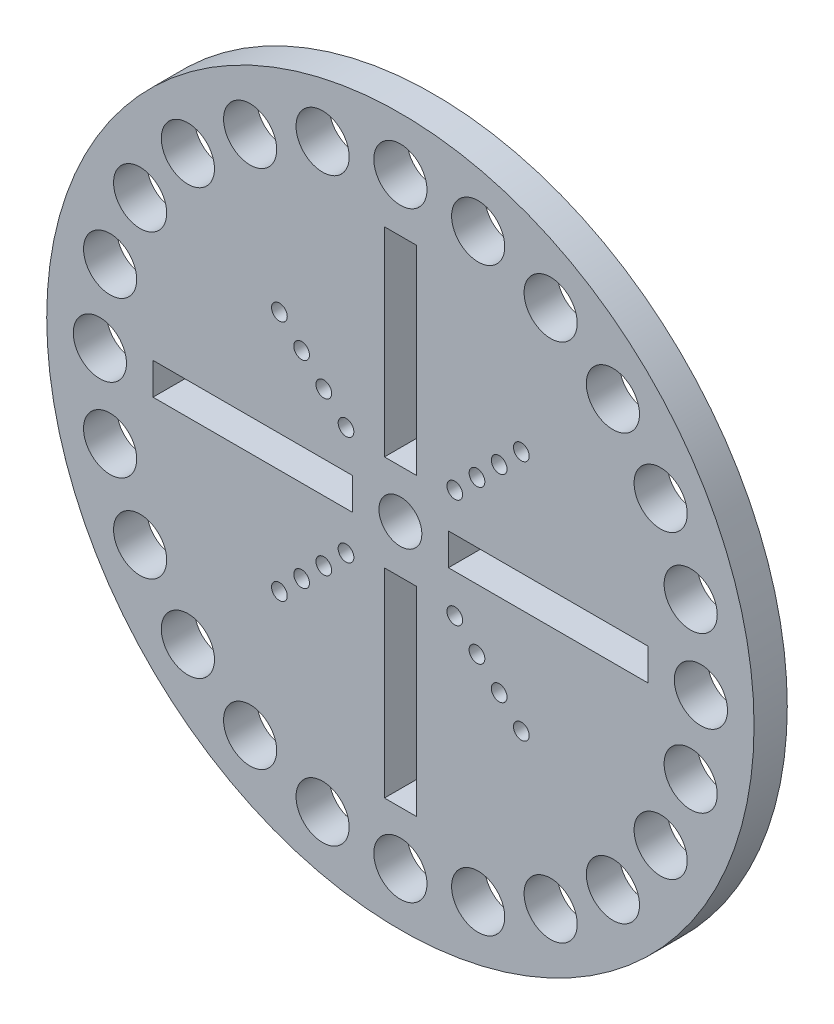
SolidWorks part; units mm, degrees
ref_plane "Front Plane" through (0, 0, 0) normal (0, 0, 1) x (1, 0, 0)
ref_plane "Top Plane" through (0, 0, 0) normal (0, 1, 0) x (1, 0, 0)
ref_plane "Right Plane" through (0, 0, 0) normal (1, 0, 0) x (0, 0, -1)
sketch "Sketch1" plane through (0, 0, 0) normal (0, 0, 1) x (1, 0, 0)
  line L0 (0, 31.26) -> (0, 33.8) construction
  line L1 (0, 28.72) -> (2.5183, 28.3885) construction
  line L2 (2.5183, 28.3885) -> (4.915, 28.0729) construction
  line L3 (4.915, 28.0729) -> (7.4333, 27.7414) construction
  line L4 (0, 2.05) -> (0, 4.59) construction
  line L5 (-0.1778, 26.1862) -> (0.1778, 26.1862) construction
  line L6 (-0.1778, 26.1862) -> (-0.1778, 30.9862) construction
  line L7 (-0.1778, 30.9862) -> (0.1778, 30.9862) construction
  line L8 (0.1778, 26.1862) -> (0.1778, 30.9862) construction
  line L9 (-1.524, 23.64) -> (1.524, 23.64)
  line L10 (-1.524, 23.64) -> (-1.524, 4.59)
  line L11 (-1.524, 4.59) -> (1.524, 4.59)
  line L12 (1.524, 23.64) -> (1.524, 4.59)
  line L13 (0, 26.18) -> (0, 23.64) construction
  line L14 (23.64, 1.524) -> (23.64, -1.524)
  line L15 (23.64, 1.524) -> (4.59, 1.524)
  line L16 (23.64, -1.524) -> (4.59, -1.524)
  line L17 (4.59, 1.524) -> (4.59, -1.524)
  line L18 (1.524, -23.64) -> (-1.524, -23.64)
  line L19 (1.524, -23.64) -> (1.524, -4.59)
  line L20 (-1.524, -23.64) -> (-1.524, -4.59)
  line L21 (1.524, -4.59) -> (-1.524, -4.59)
  line L22 (-23.64, -1.524) -> (-23.64, 1.524)
  line L23 (-23.64, -1.524) -> (-4.59, -1.524)
  line L24 (-23.64, 1.524) -> (-4.59, 1.524)
  line L25 (-4.59, -1.524) -> (-4.59, 1.524)
  line L26 (0, 0) -> (11.5612, 11.5612) construction
  line L27 (0, 0) -> (11.1701, 0) construction
  line L29 (0, 0) -> (-11.5612, 11.5612) construction
  circle A0 centre (0, 0) radius 33.8
  circle A1 centre (14.36, 24.8722) radius 2.54
  circle A2 centre (20.3081, 20.3081) radius 2.54
  circle A3 centre (24.8722, 14.36) radius 2.54
  circle A4 centre (27.7414, 7.4333) radius 2.54
  circle A5 centre (28.72, 0) radius 2.54
  circle A6 centre (27.7414, -7.4333) radius 2.54
  circle A7 centre (24.8722, -14.36) radius 2.54
  circle A8 centre (20.3081, -20.3081) radius 2.54
  circle A9 centre (14.36, -24.8722) radius 2.54
  circle A10 centre (7.4333, -27.7414) radius 2.54
  circle A11 centre (0, -28.72) radius 2.54
  circle A12 centre (-7.4333, -27.7414) radius 2.54
  circle A13 centre (-14.36, -24.8722) radius 2.54
  circle A14 centre (-20.3081, -20.3081) radius 2.54
  circle A15 centre (-24.8722, -14.36) radius 2.54
  circle A16 centre (-27.7414, -7.4333) radius 2.54
  circle A17 centre (-28.72, 0) radius 2.54
  circle A18 centre (-27.7414, 7.4333) radius 2.54
  circle A19 centre (-24.8722, 14.36) radius 2.54
  circle A20 centre (-20.3081, 20.3081) radius 2.54
  circle A21 centre (-14.36, 24.8722) radius 2.54
  circle A22 centre (-7.4333, 27.7414) radius 2.54
  circle A23 centre (0, 28.72) radius 2.54
  circle A24 centre (7.4333, 27.7414) radius 2.54
  circle A25 centre (0, 0) radius 2.05
  circle A26 centre (11.5612, 11.5612) radius 0.75
  circle A27 centre (9.4399, 9.4399) radius 0.75
  circle A28 centre (7.3186, 7.3186) radius 0.75
  circle A29 centre (5.1972, 5.1972) radius 0.75
  circle A30 centre (11.5612, -11.5612) radius 0.75
  circle A31 centre (9.4399, -9.4399) radius 0.75
  circle A32 centre (7.3186, -7.3186) radius 0.75
  circle A33 centre (5.1972, -5.1972) radius 0.75
  circle A34 centre (-11.5612, -11.5612) radius 0.75
  circle A35 centre (-9.4399, -9.4399) radius 0.75
  circle A36 centre (-7.3186, -7.3186) radius 0.75
  circle A37 centre (-5.1972, -5.1972) radius 0.75
  circle A38 centre (-11.5612, 11.5612) radius 0.75
  circle A39 centre (-9.4399, 9.4399) radius 0.75
  circle A40 centre (-7.3186, 7.3186) radius 0.75
  circle A41 centre (-5.1972, 5.1972) radius 0.75
  point P54 (0, 0)
  point P84 (0, 0)
  point P119 (0, 0)
  dimension "D1" = 5.08
  dimension "D3" = 2.54
  dimension "D5" = 4.1
  dimension "D6" = 67.6
  dimension "D4" = 3.048
  dimension "D12" = 45
  dimension "D17" = 1.5
  dimension "D18" = 4
  dimension "D8" = 4.8
  dimension "D9" = 0.3556
  dimension "D10" = 2.54
  dimension "D11" = 19.05
  dimension "D13" = 14.7
  dimension "D14" = 20.7
  dimension "D15" = 26.7
  dimension "D16" = 32.7
  dimension "D7" = 4
  dimension "D2" = 24
extrude "Boss-Extrude1" add sketch "Sketch1" along normal blind 3.175
sketch "Sketch3" [suppressed] plane through (0, 0, 0) normal (0, 0, 1) x (1, 0, 0)
  line L0 (0, 33.8) -> (0, 35.2241) construction
  line L1 (2.6941, 35.2241) -> (-2.6941, 35.2241) construction
  line L2 (-2.6941, 35.2241) -> (-4.4066, 33.5115)
  line L3 (2.6941, 35.2241) -> (4.4066, 33.5115)
  line L4 (4.4066, 33.5115) -> (-4.4066, 33.5115) construction
  arc A0 (2.6941, 35.2241) -> (-2.6941, 35.2241) centre (0, 32.53) ccw
  circle A1 centre (0, 0) radius 33.8
  arc A2 (4.4066, 33.5115) -> (-4.4066, 33.5115) centre (0, 0) ccw
  circle A3 centre (0, 0) radius 33.8 construction
  point P9 (0, 35.2241)
  dimension "D2" = 3.81
  dimension "D3" = 2.54
  dimension "D4" = 90
  dimension "D1" = 0
extrude "Boss-Extrude2" [suppressed] add sketch "Sketch3" along normal up to surface (3.175 mm away)
fillet "Fillet1" [suppressed] radius 2.54
sketch "Sketch4" plane through (0, 0, 0) normal (0, 0, 1) x (1, 0, 0)
  line L0 (-1.397, -23.513) -> (1.397, -23.513)
  line L1 (1.397, -23.513) -> (1.397, -4.717)
  line L2 (1.397, -4.717) -> (-1.397, -4.717)
  line L3 (-1.397, -4.717) -> (-1.397, -23.513)
  line L4 (-1.524, -23.64) -> (1.524, -23.64)
  line L5 (-1.524, -4.59) -> (-1.524, -23.64)
  line L6 (1.524, -4.59) -> (-1.524, -4.59)
  line L7 (1.524, -23.64) -> (1.524, -4.59)
  line L8 (-1.524, -23.64) -> (1.524, -23.64) construction
  line L9 (-1.524, -4.59) -> (-1.524, -23.64) construction
  line L10 (1.524, -4.59) -> (-1.524, -4.59) construction
  line L11 (1.524, -23.64) -> (1.524, -4.59) construction
  line L12 (23.64, -1.524) -> (23.64, 1.524)
  line L13 (4.59, -1.524) -> (23.64, -1.524)
  line L14 (4.59, 1.524) -> (4.59, -1.524)
  line L15 (23.64, 1.524) -> (4.59, 1.524)
  line L16 (23.64, -1.524) -> (23.64, 1.524) construction
  line L17 (4.59, -1.524) -> (23.64, -1.524) construction
  line L18 (4.59, 1.524) -> (4.59, -1.524) construction
  line L19 (23.64, 1.524) -> (4.59, 1.524) construction
  line L20 (1.524, 23.64) -> (-1.524, 23.64)
  line L21 (-1.524, 23.64) -> (-1.524, 4.59)
  line L22 (-1.524, 4.59) -> (1.524, 4.59)
  line L23 (1.524, 4.59) -> (1.524, 23.64)
  line L24 (1.524, 23.64) -> (-1.524, 23.64) construction
  line L25 (-1.524, 23.64) -> (-1.524, 4.59) construction
  line L26 (-1.524, 4.59) -> (1.524, 4.59) construction
  line L27 (1.524, 4.59) -> (1.524, 23.64) construction
  line L28 (-23.64, 1.524) -> (-23.64, -1.524)
  line L29 (-4.59, 1.524) -> (-23.64, 1.524)
  line L30 (-4.59, -1.524) -> (-4.59, 1.524)
  line L31 (-23.64, -1.524) -> (-4.59, -1.524)
  line L32 (-23.64, 1.524) -> (-23.64, -1.524) construction
  line L33 (-4.59, 1.524) -> (-23.64, 1.524) construction
  line L34 (-4.59, -1.524) -> (-4.59, 1.524) construction
  line L35 (-23.64, -1.524) -> (-4.59, -1.524) construction
  line L36 (23.513, -1.397) -> (23.513, 1.397)
  line L37 (23.513, 1.397) -> (4.717, 1.397)
  line L38 (4.717, 1.397) -> (4.717, -1.397)
  line L39 (4.717, -1.397) -> (23.513, -1.397)
  line L40 (1.397, 23.513) -> (-1.397, 23.513)
  line L41 (-1.397, 23.513) -> (-1.397, 4.717)
  line L42 (-1.397, 4.717) -> (1.397, 4.717)
  line L43 (1.397, 4.717) -> (1.397, 23.513)
  line L44 (-23.513, 1.397) -> (-23.513, -1.397)
  line L45 (-23.513, -1.397) -> (-4.717, -1.397)
  line L46 (-4.717, -1.397) -> (-4.717, 1.397)
  line L47 (-4.717, 1.397) -> (-23.513, 1.397)
  circle A0 centre (0, 0) radius 33.927
  circle A1 centre (28.72, 0) radius 2.54
  circle A2 centre (28.72, 0) radius 2.54 construction
  circle A3 centre (27.7414, 7.4333) radius 2.54
  circle A4 centre (27.7414, 7.4333) radius 2.54 construction
  circle A5 centre (24.8722, 14.36) radius 2.54
  circle A6 centre (24.8722, 14.36) radius 2.54 construction
  circle A7 centre (20.3081, 20.3081) radius 2.54
  circle A8 centre (20.3081, 20.3081) radius 2.54 construction
  circle A9 centre (14.36, 24.8722) radius 2.667
  circle A10 centre (14.36, 24.8722) radius 2.667 construction
  circle A11 centre (0, 0) radius 33.8
  circle A12 centre (0, 0) radius 33.8 construction
  circle A13 centre (-14.36, -24.8722) radius 2.54
  circle A14 centre (-14.36, -24.8722) radius 2.54 construction
  circle A15 centre (-7.4333, -27.7414) radius 2.54
  circle A16 centre (-7.4333, -27.7414) radius 2.54 construction
  circle A17 centre (0, -28.72) radius 2.54
  circle A18 centre (0, -28.72) radius 2.54 construction
  circle A19 centre (7.4333, -27.7414) radius 2.54
  circle A20 centre (7.4333, -27.7414) radius 2.54 construction
  circle A21 centre (14.36, -24.8722) radius 2.54
  circle A22 centre (14.36, -24.8722) radius 2.54 construction
  circle A23 centre (20.3081, -20.3081) radius 2.54
  circle A24 centre (20.3081, -20.3081) radius 2.54 construction
  circle A25 centre (24.8722, -14.36) radius 2.54
  circle A26 centre (24.8722, -14.36) radius 2.54 construction
  circle A27 centre (27.7414, -7.4333) radius 2.54
  circle A28 centre (27.7414, -7.4333) radius 2.54 construction
  circle A29 centre (-14.36, 24.8722) radius 2.54
  circle A30 centre (-14.36, 24.8722) radius 2.54 construction
  circle A31 centre (-20.3081, 20.3081) radius 2.54
  circle A32 centre (-20.3081, 20.3081) radius 2.54 construction
  circle A33 centre (-24.8722, 14.36) radius 2.54
  circle A34 centre (-24.8722, 14.36) radius 2.54 construction
  circle A35 centre (-27.7414, 7.4333) radius 2.54
  circle A36 centre (-27.7414, 7.4333) radius 2.54 construction
  circle A37 centre (-28.72, 0) radius 2.54
  circle A38 centre (-28.72, 0) radius 2.54 construction
  circle A39 centre (-27.7414, -7.4333) radius 2.54
  circle A40 centre (-27.7414, -7.4333) radius 2.54 construction
  circle A41 centre (-24.8722, -14.36) radius 2.54
  circle A42 centre (-24.8722, -14.36) radius 2.54 construction
  circle A43 centre (-20.3081, -20.3081) radius 2.54
  circle A44 centre (-20.3081, -20.3081) radius 2.54 construction
  circle A45 centre (0, 0) radius 2.05
  circle A46 centre (0, 0) radius 2.05 construction
  circle A47 centre (7.4333, 27.7414) radius 2.54
  circle A48 centre (7.4333, 27.7414) radius 2.54 construction
  circle A49 centre (0, 28.72) radius 2.54
  circle A50 centre (0, 28.72) radius 2.54 construction
  circle A51 centre (-7.4333, 27.7414) radius 2.54
  circle A52 centre (-7.4333, 27.7414) radius 2.54 construction
  circle A53 centre (28.72, 0) radius 2.413
  circle A54 centre (27.7414, 7.4333) radius 2.413
  circle A55 centre (24.8722, 14.36) radius 2.413
  circle A56 centre (20.3081, 20.3081) radius 2.413
  circle A57 centre (14.36, 24.8722) radius 2.54 construction
  circle A58 centre (-14.36, -24.8722) radius 2.413
  circle A59 centre (-7.4333, -27.7414) radius 2.413
  circle A60 centre (0, -28.72) radius 2.413
  circle A61 centre (7.4333, -27.7414) radius 2.413
  circle A62 centre (14.36, -24.8722) radius 2.413
  circle A63 centre (20.3081, -20.3081) radius 2.413
  circle A64 centre (24.8722, -14.36) radius 2.413
  circle A65 centre (27.7414, -7.4333) radius 2.413
  circle A66 centre (-14.36, 24.8722) radius 2.413
  circle A67 centre (-20.3081, 20.3081) radius 2.413
  circle A68 centre (-24.8722, 14.36) radius 2.413
  circle A69 centre (-27.7414, 7.4333) radius 2.413
  circle A70 centre (-28.72, 0) radius 2.413
  circle A71 centre (-27.7414, -7.4333) radius 2.413
  circle A72 centre (-24.8722, -14.36) radius 2.413
  circle A73 centre (-20.3081, -20.3081) radius 2.413
  circle A74 centre (0, 0) radius 1.923
  circle A75 centre (7.4333, 27.7414) radius 2.413
  circle A76 centre (0, 28.72) radius 2.413
  circle A77 centre (-7.4333, 27.7414) radius 2.413
  circle A78 centre (14.36, 24.8722) radius 2.413
  circle A79 centre (-5.1972, -5.1972) radius 0.75 construction
  circle A80 centre (-7.3186, -7.3186) radius 0.75 construction
  circle A81 centre (-9.4399, -9.4399) radius 0.75 construction
  circle A82 centre (-11.5612, -11.5612) radius 0.75 construction
  circle A83 centre (5.1972, -5.1972) radius 0.75 construction
  circle A84 centre (7.3186, -7.3186) radius 0.75 construction
  circle A85 centre (9.4399, -9.4399) radius 0.75 construction
  circle A86 centre (11.5612, -11.5612) radius 0.75 construction
  circle A87 centre (11.5612, 11.5612) radius 0.75 construction
  circle A88 centre (9.4399, 9.4399) radius 0.75 construction
  circle A89 centre (7.3186, 7.3186) radius 0.75 construction
  circle A90 centre (5.1972, 5.1972) radius 0.75 construction
  circle A91 centre (-5.1972, 5.1972) radius 0.75 construction
  circle A92 centre (-7.3186, 7.3186) radius 0.75 construction
  circle A93 centre (-9.4399, 9.4399) radius 0.75 construction
  circle A94 centre (-11.5612, 11.5612) radius 0.75 construction
  circle A95 centre (-5.1972, -5.1972) radius 0.75 construction
  circle A96 centre (-7.3186, -7.3186) radius 0.75 construction
  circle A97 centre (-9.4399, -9.4399) radius 0.75 construction
  circle A98 centre (-11.5612, -11.5612) radius 0.75 construction
  circle A99 centre (5.1972, -5.1972) radius 0.75 construction
  circle A100 centre (7.3186, -7.3186) radius 0.75 construction
  circle A101 centre (9.4399, -9.4399) radius 0.75 construction
  circle A102 centre (11.5612, -11.5612) radius 0.75 construction
  circle A103 centre (11.5612, 11.5612) radius 0.75 construction
  circle A104 centre (9.4399, 9.4399) radius 0.75 construction
  circle A105 centre (7.3186, 7.3186) radius 0.75 construction
  circle A106 centre (5.1972, 5.1972) radius 0.75 construction
  circle A107 centre (-5.1972, 5.1972) radius 0.75 construction
  circle A108 centre (-7.3186, 7.3186) radius 0.75 construction
  circle A109 centre (-9.4399, 9.4399) radius 0.75 construction
  circle A110 centre (-11.5612, 11.5612) radius 0.75 construction
  circle A111 centre (11.5612, 11.5612) radius 0.623
  circle A112 centre (9.4399, 9.4399) radius 0.623
  circle A113 centre (7.3186, 7.3186) radius 0.623
  circle A114 centre (5.1972, 5.1972) radius 0.623
  circle A115 centre (-5.1972, 5.1972) radius 0.623
  circle A116 centre (-7.3186, 7.3186) radius 0.623
  circle A117 centre (-9.4399, 9.4399) radius 0.623
  circle A118 centre (-11.5612, 11.5612) radius 0.623
  circle A119 centre (5.1972, -5.1972) radius 0.623
  circle A120 centre (7.3186, -7.3186) radius 0.623
  circle A121 centre (9.4399, -9.4399) radius 0.623
  circle A122 centre (11.5612, -11.5612) radius 0.623
  circle A123 centre (-5.1972, -5.1972) radius 0.623
  circle A124 centre (-7.3186, -7.3186) radius 0.623
  circle A125 centre (-9.4399, -9.4399) radius 0.623
  circle A126 centre (-11.5612, -11.5612) radius 0.623
  dimension "D1" = 0
  dimension "D2" = 0
  dimension "D3" = 0
  dimension "D4" = 0
  dimension "D5" = 0.127
  dimension "D6" = 0
  dimension "D7" = 0
  dimension "D8" = 0
  dimension "D9" = 0
  dimension "D10" = 0
  dimension "D11" = 0
  dimension "D12" = 0
  dimension "D13" = 0
  dimension "D14" = 0
  dimension "D15" = 0
  dimension "D16" = 0
  dimension "D17" = 0
  dimension "D18" = 0
  dimension "D19" = 0
  dimension "D20" = 0
  dimension "D21" = 0
  dimension "D22" = 0
  dimension "D23" = 0
  dimension "D24" = 0
  dimension "D25" = 0
  dimension "D26" = 0
  dimension "D27" = 0
  dimension "D28" = 0
  dimension "D29" = 0
  dimension "D30" = 0
  dimension "D31" = 0.127
  dimension "D32" = 0.127
  dimension "D33" = 0.127
  dimension "D34" = 0.127
extrude "Kerf Adjustment" [suppressed] add sketch "Sketch4" along normal blind 3.175
equation "\"kerf_adjustment\"= .005"
equation "\"D32@Sketch4\"= \"kerf_adjustment\""
equation "\"D31@Sketch4\" = \"kerf_adjustment\""
equation "\"D33@Sketch4\"= \"kerf_adjustment\""
